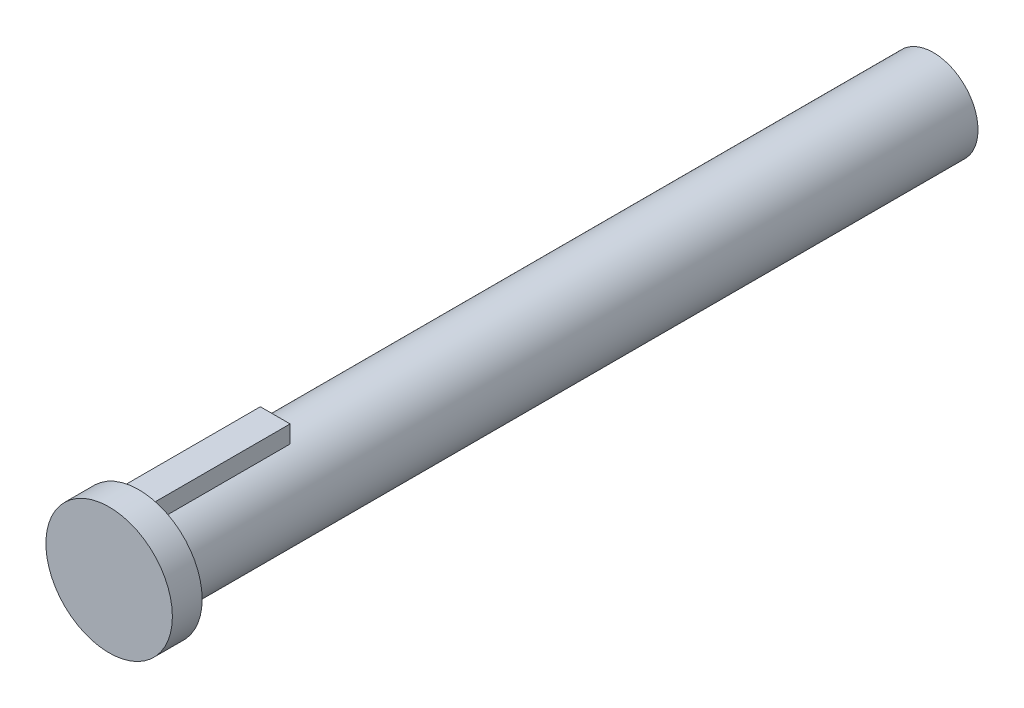
SolidWorks part; units mm, degrees
ref_plane "Front Plane" through (0, 0, 0) normal (0, 0, 1) x (1, 0, 0)
ref_plane "Top Plane" through (0, 0, 0) normal (0, 1, 0) x (1, 0, 0)
ref_plane "Right Plane" through (0, 0, 0) normal (1, 0, 0) x (0, 0, -1)
sketch "Sketch1" plane through (0, 0, 0) normal (0, 0, 1) x (1, 0, 0)
  circle A0 centre (0, 0) radius 3
  dimension "D1" = 6
extrude "Boss-Extrude1" add sketch "Sketch1" along normal blind 53.38
sketch "Sketch2" plane through (0, 0, 53.38) normal (0, 0, 1) x (1, 0, 0)
  line L0 (-1, 2.8284) -> (-1, 3.9984)
  line L1 (-1, 3.9984) -> (1, 3.9984)
  line L2 (1, 3.9984) -> (1, 2.8284)
  line L3 (-1, 2.8284) -> (1, 2.8284)
  circle A0 centre (0, 0) radius 3 construction
  dimension "D1" = 1.17
  dimension "D2" = 2
  dimension "D3" = 1.17
extrude "Boss-Extrude2" add sketch "Sketch2" against normal blind 9.16
sketch "Sketch3" plane through (0, 0, 53.38) normal (0, 0, 1) x (1, 0, 0)
  circle A0 centre (0, 0) radius 4.25
  dimension "D1" = 8.5
extrude "Boss-Extrude3" add sketch "Sketch3" along normal blind 2
